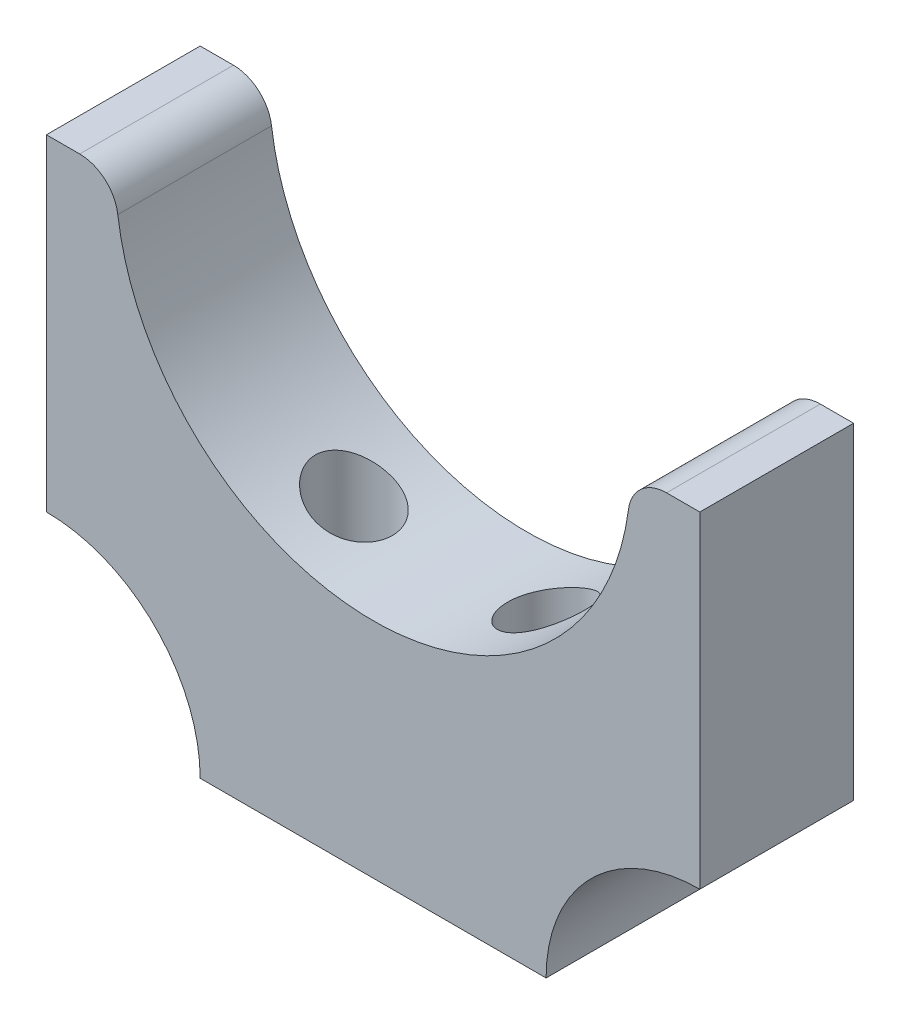
SolidWorks part; units mm, degrees
ref_plane "Plan de face" through (0, 0, 0) normal (0, 0, 1) x (1, 0, 0)
ref_plane "Plan de dessus" through (0, 0, 0) normal (0, 1, 0) x (1, 0, 0)
ref_plane "Plan de droite" through (0, 0, 0) normal (1, 0, 0) x (0, 0, -1)
sketch "Esquisse1" plane through (0, 0, 0) normal (0, 0, 1) x (1, 0, 0)
  line L0 (0, 12.5) -> (0, -12.5) construction
  line L1 (17, 12.5) -> (-17, 12.5) construction
  line L2 (17, 12.5) -> (17, -12.5) construction
  line L3 (17, -12.5) -> (-17, -12.5) construction
  line L4 (-17, 12.5) -> (-17, -12.5) construction
  line L5 (17, 12.5) -> (-17, -12.5) construction
  line L6 (17, -12.5) -> (-17, 12.5) construction
  line L7 (-17, 12.5) -> (-17, -4.5)
  line L8 (-9, -12.5) -> (9, -12.5)
  line L9 (17, -4.5) -> (17, 12.5)
  line L10 (-13.4, 12.5) -> (-17, 12.5)
  line L11 (13.4, 12.5) -> (17, 12.5)
  circle A0 centre (0, 12.5) radius 13.4 construction
  arc A1 (-17, -4.5) -> (-9, -12.5) centre (-17, -12.5) cw
  arc A2 (17, -4.5) -> (9, -12.5) centre (17, -12.5) ccw
  arc A3 (-13.4, 12.5) -> (13.4, 12.5) centre (0, 12.5) ccw
  point P0 (0, 0)
  dimension "D3" = 26.8
  dimension "D1" = 34
  dimension "D2" = 25
  dimension "D4" = 8
extrude "Boss.-Extru.1" add sketch "Esquisse1" along normal blind 8
sketch "Esquisse2" plane through (0, -12.5, 0) normal (0, -1, 0) x (1, 0, 0)
  line L0 (0, 0) -> (0, 8) construction
  line L1 (-9, 8) -> (9, 8) construction
  line L2 (-5, 4) -> (5, 4) construction
  line L3 (-9, 8) -> (-9, 0) construction
  circle A0 centre (-5, 4) radius 2
  circle A1 centre (5, 4) radius 2
  point P8 (0, 4)
  dimension "D1" = 4
  dimension "D2" = 4
extrude "Enlèv. mat.-Extru.1" cut sketch "Esquisse2" against normal up to next
chamfer "Chanfrein1" distance 1 angle 45 2 edges at (5, -12.5, 2) (-5, -12.5, 2)
fillet "Congé1" radius 2 2 edges at (13.4, 12.5, 4) (-13.4, 12.5, 4)
